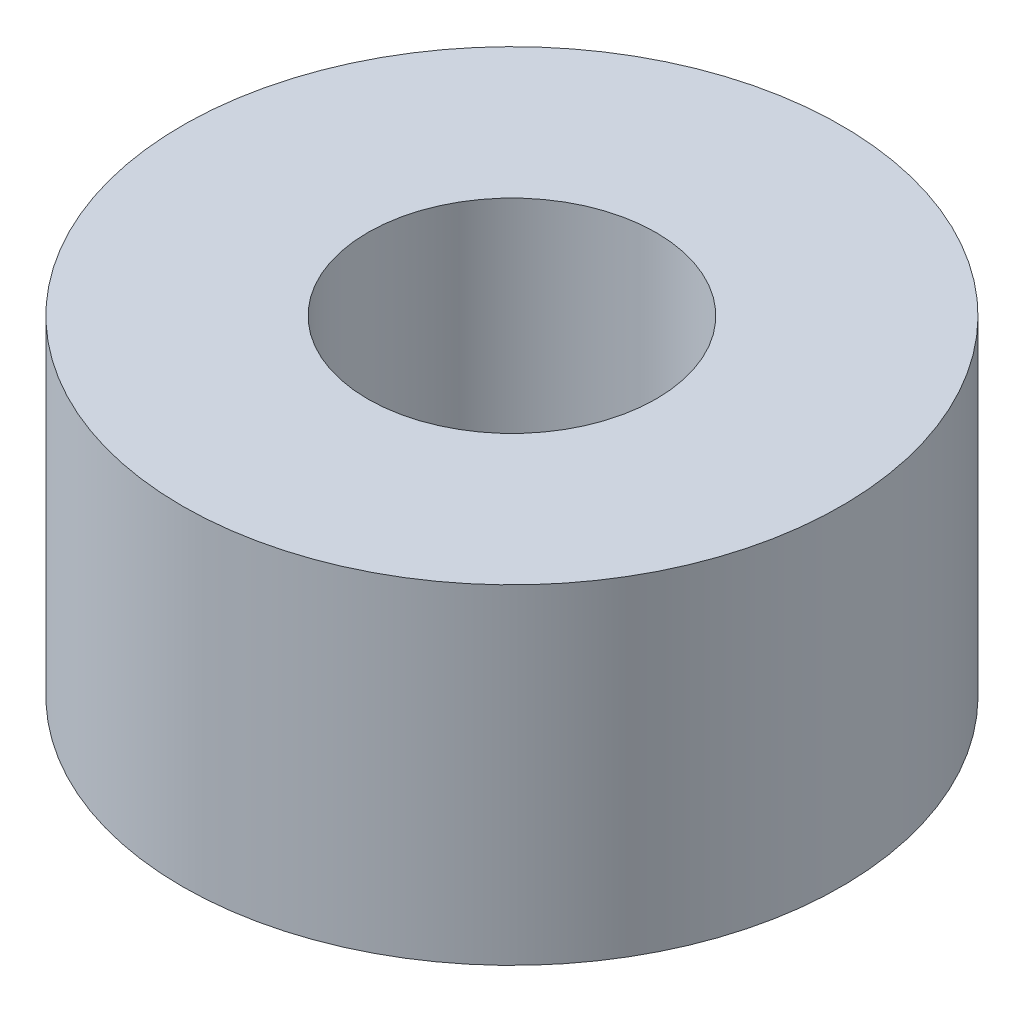
SolidWorks part; units mm, degrees
ref_plane "Спереди" through (0, 0, 0) normal (0, 0, 1) x (1, 0, 0)
ref_plane "Сверху" through (0, 0, 0) normal (0, 1, 0) x (1, 0, 0)
ref_plane "Справа" through (0, 0, 0) normal (1, 0, 0) x (0, 0, -1)
sketch "Эскиз1" plane through (0, 0, 0) normal (0, 1, 0) x (1, 0, 0)
  circle A0 centre (0, 0) radius 4
  circle A1 centre (0, 0) radius 1.75
  dimension "D1" = 3.5
  dimension "D2" = 8
extrude "Бобышка-Вытянуть1" add sketch "Эскиз1" along normal blind 4
